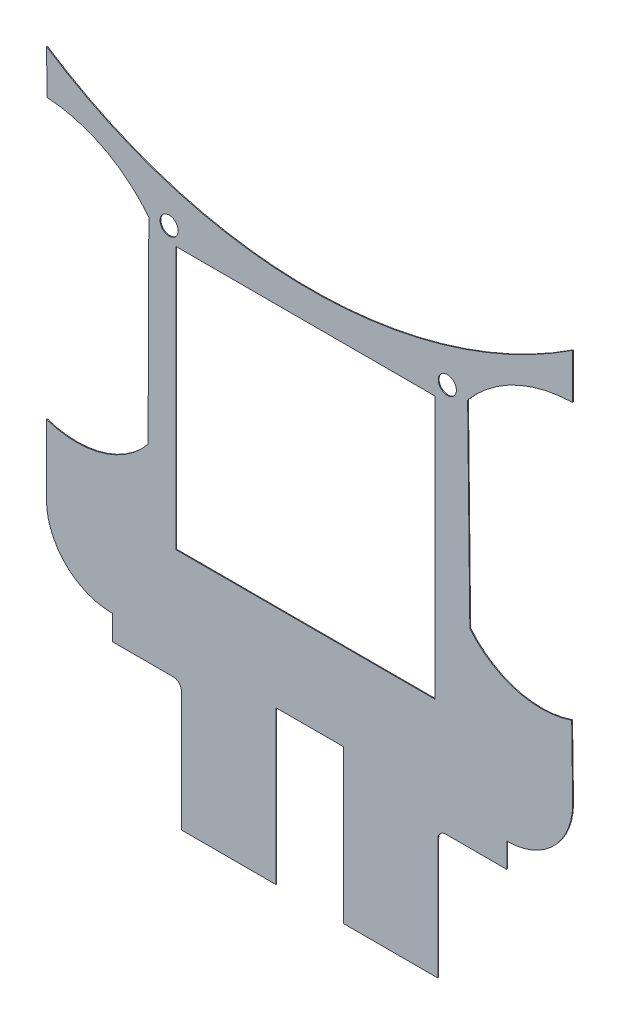
SolidWorks part; units mm, degrees
ref_plane "Alzado" through (0, 0, 0) normal (0, 0, 1) x (1, 0, 0)
ref_plane "Planta" through (0, 0, 0) normal (0, 1, 0) x (1, 0, 0)
ref_plane "Vista lateral" through (0, 0, 0) normal (1, 0, 0) x (0, 0, -1)
sketch "Model" plane through (0, 0, 0) normal (0, 0, 1) x (1, 0, 0)
  line L0 (50.7907, 26.2002) -> (35.504, 26.2002)
  line L1 (50.7907, -5.7998) -> (50.7907, 26.2002)
  line L2 (19.2174, -5.7998) -> (50.7907, -5.7998)
  line L3 (19.2174, 26.2002) -> (19.2174, -5.7998)
  line L4 (35.504, 26.2002) -> (19.2174, 26.2002)
  line L5 (51.1434, -20.3853) -> (51.1434, -35.0531)
  line L6 (59.5626, -19.3853) -> (52.1199, -19.3853)
  line L7 (59.5626, -17.3853) -> (59.5626, -19.3853)
  line L8 (31.411, -16.3861) -> (31.411, -35.0531)
  line L9 (39.6329, -16.3861) -> (31.411, -16.3861)
  line L10 (39.6329, -35.0531) -> (39.6329, -16.3861)
  line L11 (67.4637, 0.3131) -> (67.5887, -8.492)
  line L12 (3.4553, -8.3861) -> (3.4553, 0.0719)
  line L13 (59.5626, -16.3853) -> (59.5626, -17.3853)
  line L14 (59.6953, -16.3853) -> (59.5626, -16.3853)
  line L15 (11.4814, -16.3861) -> (11.3487, -16.3861)
  line L16 (11.4814, -19.3861) -> (11.4814, -16.3861)
  line L17 (18.9139, -19.3861) -> (11.4814, -19.3861)
  line L18 (19.9006, -35.0531) -> (19.9006, -20.3861)
  line L19 (54.7827, 27.7724) -> (55.0521, 3.7752)
  line L20 (15.929, 27.626) -> (15.8405, 3.6274)
  line L21 (19.9006, -35.0531) -> (31.411, -35.0531)
  line L22 (51.1434, -35.0531) -> (39.6329, -35.0531)
  line L23 (3.4553, 39.4184) -> (3.5457, 34.0653)
  line L24 (67.5887, 33.9134) -> (67.5887, 39.4184)
  arc A0 (52.1199, -19.3853) -> (51.1434, -20.3853) centre (52.1368, -20.3786) ccw
  arc A2 (59.6953, -16.3853) -> (67.5887, -8.3853) centre (59.642, -8.4387) ccw
  arc A3 (3.4553, -8.3861) -> (11.3487, -16.3861) centre (11.402, -8.4395) ccw
  arc A4 (19.9006, -20.3861) -> (18.9139, -19.3861) centre (18.9073, -20.3795) ccw
  circle A5 centre (52.3068, 28.1183) radius 1.1055
  circle A6 centre (18.4022, 27.9905) radius 1.1055
  arc A7 (55.0521, 3.7752) -> (67.4637, 0.3131) centre (63.7463, 10.9652) ccw
  arc A8 (67.5887, 33.9134) -> (54.7827, 27.7724) centre (67.9925, 16.6483) ccw
  arc A9 (15.929, 27.626) -> (3.5457, 34.0653) centre (2.5998, 17.1196) ccw
  arc A10 (3.4553, 0.0719) -> (15.8405, 3.6274) centre (7.0923, 10.7517) ccw
  arc A11 (3.4553, 39.4184) -> (67.5887, 39.4184) centre (35.522, 88.1034) ccw
extrude "Saliente-Extruir1" add sketch "Model" along normal blind 0.1 contours A11 L23 A9 L20 A10 L12 A3 L15 L16 L17 A4 L18 L21 L8 L9 L10 L22 L5 A0 L6 L7 L13 L14 A2 L11 A7 L19 A8 L24 A6 A5 L4 L0 L1 L2 L3
